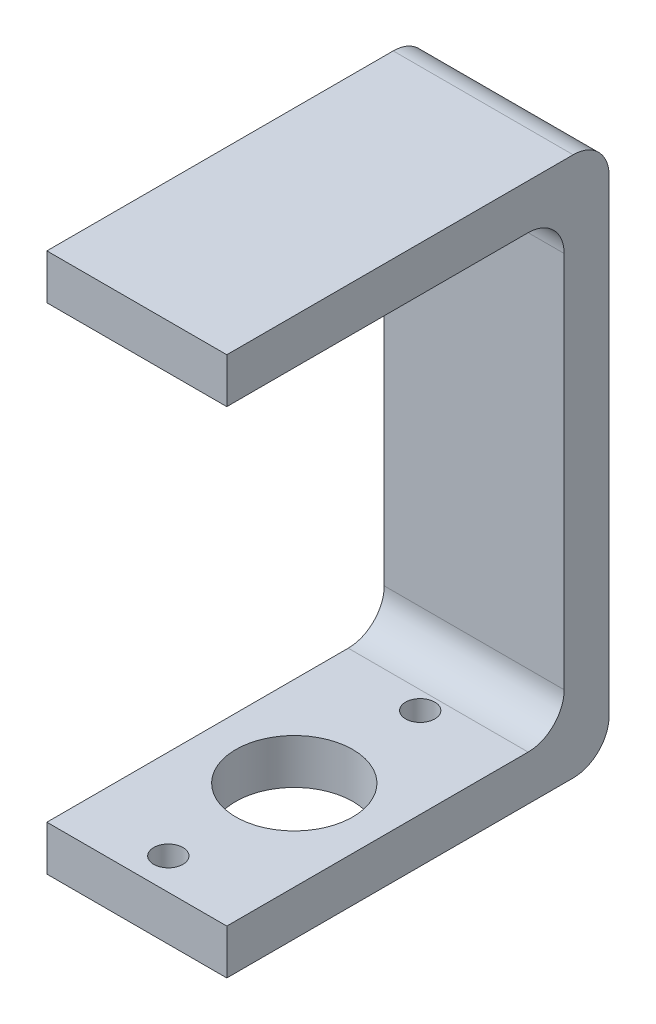
SolidWorks part; units mm, degrees
material "1060 合金"
ref_plane "前视基准面" through (0, 0, 0) normal (0, 0, 1) x (1, 0, 0)
ref_plane "上视基准面" through (0, 0, 0) normal (0, 1, 0) x (1, 0, 0)
ref_plane "右视基准面" through (0, 0, 0) normal (1, 0, 0) x (0, 0, -1)
sketch "草图1" plane through (0, 0, 0) normal (1, 0, 0) x (0, 0, -1)
  line L0 (0, 0) -> (77, 0)
  line L1 (85, 8) -> (85, 112)
  line L2 (77, 120) -> (0, 120)
  line L3 (0, 120) -> (0, 110)
  line L4 (0, 110) -> (67, 110)
  line L5 (75, 102) -> (75, 18)
  line L6 (67, 10) -> (0, 10)
  line L7 (0, 10) -> (0, 0)
  arc A0 (67, 10) -> (75, 18) centre (67, 18) ccw
  arc A1 (75, 102) -> (67, 110) centre (67, 102) ccw
  arc A2 (85, 8) -> (77, 0) centre (77, 8) cw
  arc A3 (85, 112) -> (77, 120) centre (77, 112) ccw
  point P11 (75, 10)
  point P14 (75, 110)
  point P17 (85, 0)
  point P20 (85, 120)
  dimension "D7" = 8
  dimension "D1" = 85
  dimension "D2" = 75
  dimension "D3" = 10
  dimension "D5" = 100
  dimension "D6" = 10
extrude "凸台-拉伸1" add sketch "草图1" along normal blind 40
sketch "草图5" plane through (0, 0, 0) normal (0, -1, 0) x (1, 0, 0)
  line L0 (20, 0) -> (20, -70) construction
  line L1 (40, 0) -> (0, 0) construction
  circle A0 centre (20, -35) radius 13
  circle A1 centre (20, -35) radius 28 construction
  dimension "D1" = 26
  dimension "D3" = 56
  dimension "D2" = 35
extrude "切除-拉伸1" cut sketch "草图5" against normal up to next
sketch "草图6" plane through (0, 0, 0) normal (0, -1, 0) x (1, 0, 0)
  line L0 (20, -7) -> (20, -35) construction
  circle A0 centre (20, -7) radius 3.25
  circle A1 centre (20, -63) radius 3.25
  dimension "D1" = 6.5
  dimension "D2" = 6.5
  dimension "D3" = 56
  dimension "D4" = 28
extrude "切除-拉伸2" cut sketch "草图6" against normal blind 20
